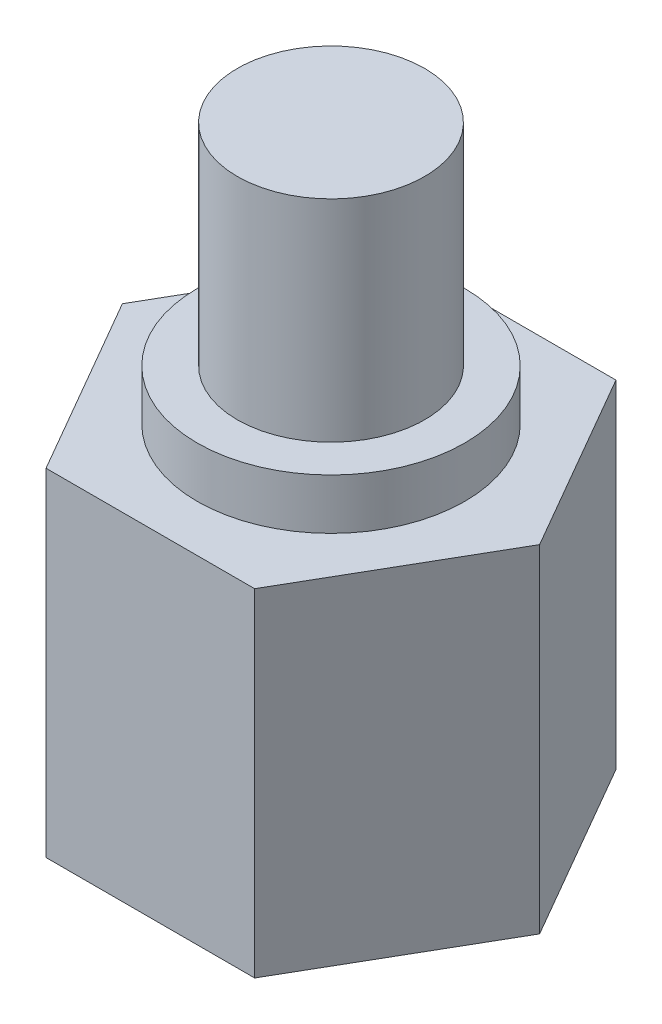
SolidWorks part; units mm, degrees
ref_plane "Front Plane" through (0, 0, 0) normal (0, 0, 1) x (1, 0, 0)
ref_plane "Top Plane" through (0, 0, 0) normal (0, 1, 0) x (1, 0, 0)
ref_plane "Right Plane" through (0, 0, 0) normal (1, 0, 0) x (0, 0, -1)
sketch "Sketch1" plane through (0, 0, 0) normal (0, 1, 0) x (1, 0, 0)
  line L1 (24.75, 0) -> (12.375, 21.4341)
  line L2 (12.375, 21.4341) -> (-12.375, 21.4341)
  line L3 (-12.375, 21.4341) -> (-24.75, 0)
  line L4 (-24.75, 0) -> (-12.375, -21.4341)
  line L5 (-12.375, -21.4341) -> (12.375, -21.4341)
  line L6 (12.375, -21.4341) -> (24.75, 0)
  circle A0 centre (0, 0) radius 21.4341 construction
extrude "Boss-Extrude1" add sketch "Sketch1" along normal blind 40 separate body
sketch "Sketch2" plane through (0, 40, 0) normal (0, 1, 0) x (1, 0, 0)
  circle A0 centre (0, 0) radius 15.875
extrude "Boss-Extrude2" add sketch "Sketch2" along normal blind 6 separate body
sketch "Sketch3" plane through (0, 46, 0) normal (0, 1, 0) x (1, 0, 0)
  circle A0 centre (0, 0) radius 11.1125
extrude "Boss-Extrude3" add sketch "Sketch3" along normal blind 25 separate body
sketch "Sketch4" plane through (0, 0, 0) normal (0, -1, 0) x (1, 0, 0)
  circle A0 centre (0, 0) radius 7.5
extrude "Cut-Extrude1" cut sketch "Sketch4" against normal blind 25
